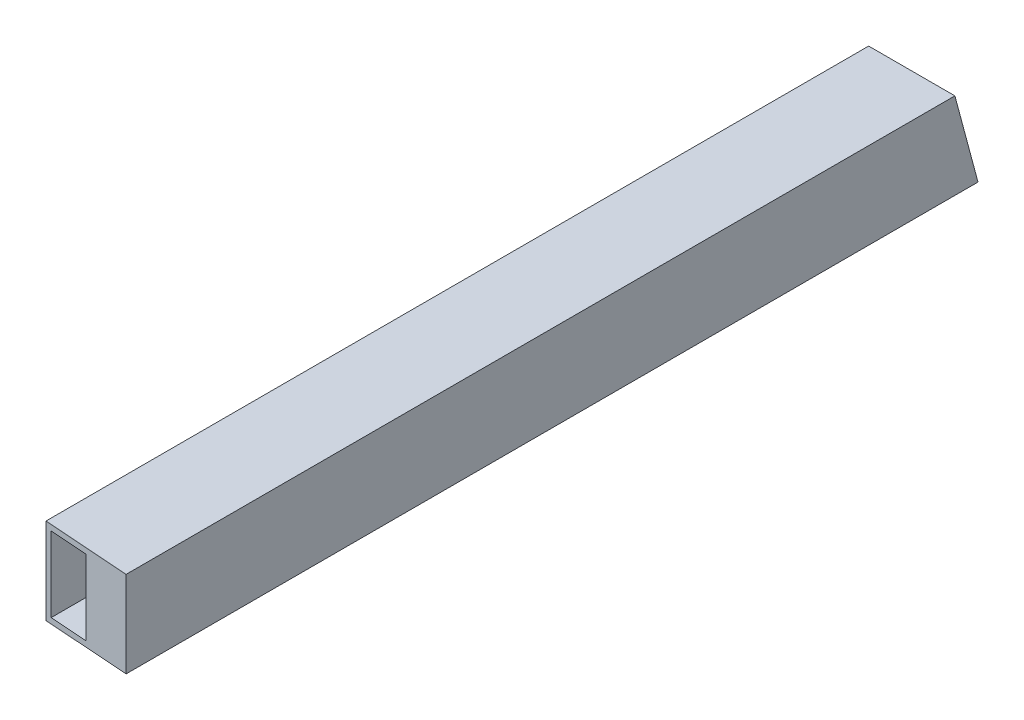
SolidWorks part; units mm, degrees
ref_plane "Front Plane" through (0, 0, 0) normal (0, 0, 1) x (1, 0, 0)
ref_plane "Top Plane" through (0, 0, 0) normal (0, 1, 0) x (1, 0, 0)
ref_plane "Right Plane" through (0, 0, 0) normal (1, 0, 0) x (0, 0, -1)
sketch "Sketch1" plane through (0, 0, 0) normal (0, 0, 1) x (1, 0, 0)
  line L1 (11.049, 11.049) -> (-11.049, 11.049)
  line L2 (11.049, 11.049) -> (11.049, -11.049)
  line L3 (11.049, -11.049) -> (-11.049, -11.049)
  line L4 (-11.049, 11.049) -> (-11.049, -11.049)
  line L5 (11.049, 11.049) -> (-11.049, -11.049) construction
  line L6 (11.049, -11.049) -> (-11.049, 11.049) construction
  line L7 (12.7, 12.7) -> (-12.7, 12.7)
  line L8 (12.7, 12.7) -> (12.7, -12.7)
  line L9 (12.7, -12.7) -> (-12.7, -12.7)
  line L10 (-12.7, 12.7) -> (-12.7, -12.7)
  line L11 (12.7, 12.7) -> (-12.7, -12.7) construction
  line L12 (12.7, -12.7) -> (-12.7, 12.7) construction
  point P0 (0, 0)
  point P6 (0, 0)
  dimension "D3" = 1.651
  dimension "D4" = 1.651
  dimension "D5" = 1.651
  dimension "D2" = 25.4
  dimension "D1" = 25.4
extrude "Boss-Extrude1" add sketch "Sketch1" along normal up to vertex (250 mm away)
sketch "Sketch3" plane through (0, 0, 0) normal (0, 1, 0) x (1, 0, 0)
  line L0 (0, 12.8662) -> (0, -262.1311) construction
  line L1 (0, -13.97) -> (0, 13.97) construction
ref_point "Point1"
sketch "Sketch4" plane through (0, 0, 250) normal (0, 0, 1) x (1, 0, 0)
  line L4 (-12.7, 12.7) -> (-12.7, -12.7)
  line L5 (-12.7, -12.7) -> (12.7, -12.7)
  line L6 (12.7, -12.7) -> (12.7, 12.7)
  line L7 (12.7, 12.7) -> (-12.7, 12.7)
  line L8 (-12.7, 12.7) -> (-12.7, -12.7)
  line L9 (-12.7, -12.7) -> (12.7, -12.7)
  line L10 (12.7, -12.7) -> (12.7, 12.7)
  line L11 (12.7, 12.7) -> (-12.7, 12.7)
  dimension "D1" = 0
extrude "Boss-Extrude2" add sketch "Sketch4" along normal blind 25.4
sketch "Sketch5" plane through (-589.3194, -151.3216, 111.9717) normal (0, 1, 0) x (0, 0, -1)
  line L3 (-140.2463, -620.2998) -> (-118.0283, -589.3194) construction
  line L4 (-140.2463, -620.2998) -> (-213.0168, -571.7281)
  line L5 (124.8378, -589.3194) -> (-150.1594, -589.3194) construction
  line L6 (-213.0168, -571.7281) -> (-135.8103, -558.3389)
  line L7 (-140.2463, -620.2998) -> (-157.8243, -586.4703) construction
  line L8 (-125.2934, -591.1522) -> (-397.4859, -551.9772) construction
  line L9 (-48.7365, -602.1706) -> (-227.3201, -576.4681) construction
  line L10 (-140.2463, -620.2998) -> (-135.8103, -558.3389)
  dimension "D1" = 20
  dimension "D2" = 20
extrude "Cut-Extrude1" cut sketch "Sketch5" along normal through all
sketch "Sketch6" plane through (12.7, 0, 0) normal (1, 0, 0) x (0, 0, -1)
  line L0 (0, -12.7) -> (-11.4958, 30.2028)
  line L1 (-11.4958, 30.2028) -> (0, 24.0931)
  line L2 (0, 24.0931) -> (0, -12.7)
  dimension "D1" = 15
extrude "Cut-Extrude2" cut sketch "Sketch6" against normal through all
equation "\"c1c2Len\"= 250"
equation "\"1inchSquareTubeLen\"=25.4"
equation "\"D2@Sketch1\"=\"1inchSquareTubeLen\""
equation "\"D1@Sketch1\"=\"1inchSquareTubeLen\""
equation "\"squareTubeWallThickness\"=1.651"
equation "\"D5@Sketch1\"=\"squareTubeWallThickness\""
equation "\"D4@Sketch1\"=\"squareTubeWallThickness\""
equation "\"D3@Sketch1\"=\"squareTubeWallThickness\""
